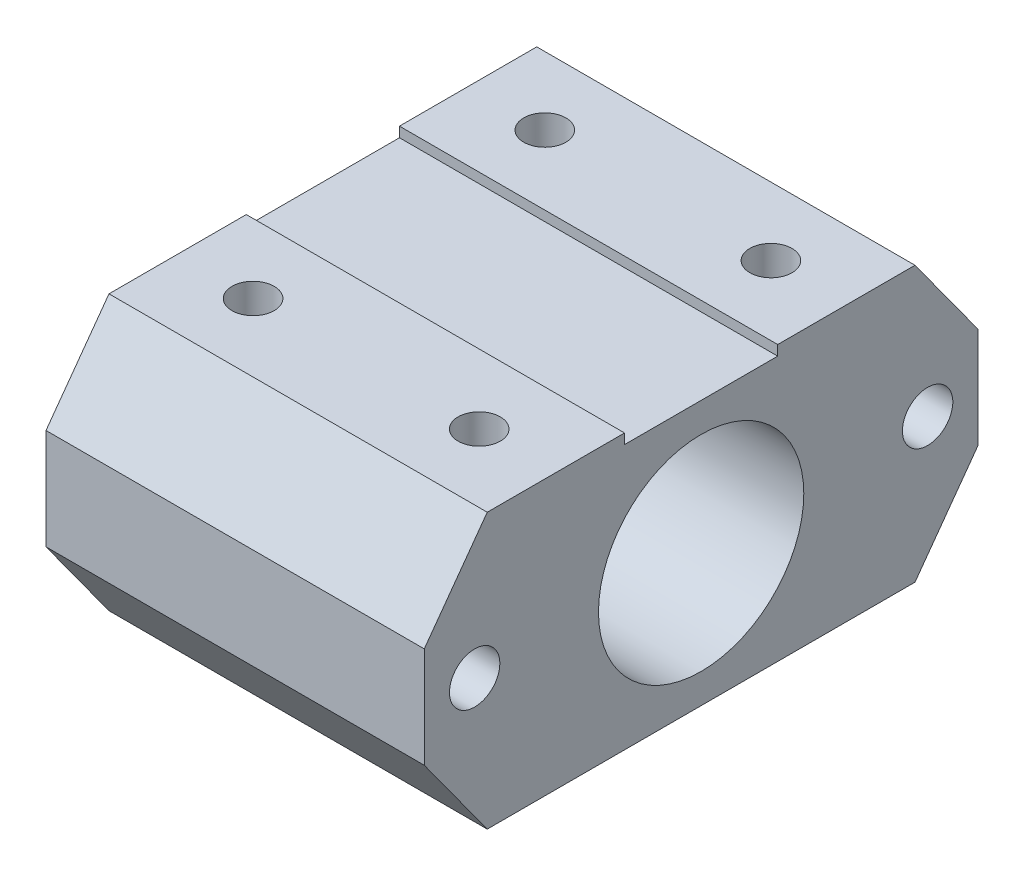
SolidWorks part; units mm, degrees
ref_plane "Front Plane" through (0, 0, 0) normal (0, 0, 1) x (1, 0, 0)
ref_plane "Top Plane" through (0, 0, 0) normal (0, 1, 0) x (1, 0, 0)
ref_plane "Right Plane" through (0, 0, 0) normal (1, 0, 0) x (0, 0, -1)
sketch "Sketch1" plane through (0, 0, 0) normal (0, 1, 0) x (1, 0, 0)
  line L0 (15.015, 33.96) -> (15.015, 0) construction
  line L1 (0, 0) -> (30.03, 0)
  line L2 (0, 0) -> (0, 33.96)
  line L3 (0, 33.96) -> (30.03, 33.96)
  line L4 (30.03, 0) -> (30.03, 33.96)
  line L5 (0, 28.56) -> (30.03, 28.56) construction
  line L6 (23.99, 33.96) -> (23.99, 0) construction
  line L7 (0, 16.98) -> (30.03, 16.98) construction
  circle A0 centre (23.99, 28.56) radius 1.675
  circle A1 centre (6.04, 28.56) radius 1.675
  circle A2 centre (23.99, 5.4) radius 1.675
  circle A3 centre (6.04, 5.4) radius 1.675
  dimension "D5" = 3.35
  dimension "D1" = 33.96
  dimension "D2" = 30.03
  dimension "D3" = 6.04
  dimension "D4" = 5.4
extrude "Boss-Extrude4" add sketch "Sketch1" along normal blind 21.79
sketch "Sketch5" plane through (30.03, 0, 0) normal (1, 0, 0) x (0, 0, -1)
  line L0 (33.96, 10.5) -> (0, 10.5) construction
  line L1 (33.96, 21.79) -> (33.96, 0) construction
  line L2 (0, 21.79) -> (0, 0) construction
  line L3 (0, 0) -> (33.96, 0) construction
  circle A0 centre (16.98, 10.5) radius 8.15
  dimension "D2" = 16.3
  dimension "D1" = 10.5
extrude "Cut-Extrude1" cut sketch "Sketch5" against normal through all
sketch "Sketch7" plane through (0, 21.79, 0) normal (0, 1, 0) x (1, 0, 0)
  line L0 (0, 33.96) -> (0, 0) construction
  line L1 (0, 23.06) -> (30.03, 23.06)
  line L2 (0, 23.06) -> (0, 10.9)
  line L3 (0, 10.9) -> (30.03, 10.9)
  line L4 (30.03, 23.06) -> (30.03, 10.9)
  line L5 (30.03, 33.96) -> (0, 33.96) construction
  line L6 (0, 0) -> (30.03, 0) construction
  line L7 (30.03, 0) -> (30.03, 33.96) construction
  dimension "D1" = 10.9
  dimension "D2" = 10.9
extrude "Cut-Extrude2" cut sketch "Sketch7" against normal blind 0.8
sketch "Sketch10" plane through (0, 0, 0) normal (-1, 0, 0) x (0, 0, 1)
  circle A0 centre (-16.98, 10.5) radius 8.15
  circle A1 centre (-16.98, 10.5) radius 8.15 construction
  circle A2 centre (-16.98, 10.5) radius 4.75
  dimension "D1" = 9.5
extrude "Boss-Extrude6" add sketch "Sketch10" against normal blind 3
sketch "Sketch12" plane through (0, 0, 0) normal (-1, 0, 0) x (0, 0, 1)
  line L0 (0, 10.895) -> (-33.96, 10.895) construction
  line L1 (0, 21.79) -> (0, 0) construction
  line L2 (-33.96, 21.79) -> (-33.96, 0) construction
  line L3 (5, 14.895) -> (0, 21.79)
  line L5 (-33.96, 14.895) -> (-33.96, 6.895)
  line L7 (-38.96, 14.895) -> (-38.96, 6.895)
  line L9 (0, 14.895) -> (0, 6.895)
  line L11 (5, 14.895) -> (5, 6.895)
  line L12 (0, 21.79) -> (0, 14.895)
  line L13 (5, 6.895) -> (0, 0)
  line L14 (0, 0) -> (0, 6.895)
  line L15 (-33.96, 14.895) -> (-33.96, 21.79)
  line L16 (-33.96, 21.79) -> (-38.96, 14.895)
  line L17 (-33.96, 6.895) -> (-33.96, 0)
  line L18 (-33.96, 0) -> (-38.96, 6.895)
  point P14 (0, 10.895)
  point P15 (-33.96, 10.895)
  dimension "D1" = 5
  dimension "D2" = 8
  dimension "D3" = 5
extrude "Boss-Extrude7" add sketch "Sketch12" against normal up to surface (30.03 mm away) up to face at (30.03, 16.1425, -16.98)
sketch "Sketch13" plane through (30.03, 0, 0) normal (1, 0, 0) x (0, 0, -1)
  line L0 (16.98, 20.99) -> (16.98, 0) construction
  line L1 (10.9, 20.99) -> (23.06, 20.99) construction
  line L2 (-5, 14.895) -> (-5, 6.895) construction
  line L3 (0, 0) -> (33.96, 0) construction
  line L4 (-5, 10.895) -> (38.96, 10.895) construction
  line L5 (38.96, 6.895) -> (38.96, 14.895) construction
  circle A0 centre (-1, 10.895) radius 2
  circle A1 centre (34.96, 10.895) radius 2
  dimension "D2" = 4
  dimension "D1" = 4
extrude "Cut-Extrude4" cut sketch "Sketch13" against normal blind 10
equation "\"8mm hole\" = 8.4mm"
equation "\"22mm hole\"= 23mm"
equation "\"15mm hole\"= 15.8mm"
equation "\"bed height offset\"= 3mm"
equation "\"D2@Sketch5\"=\"15mm hole\" + 0.5"
